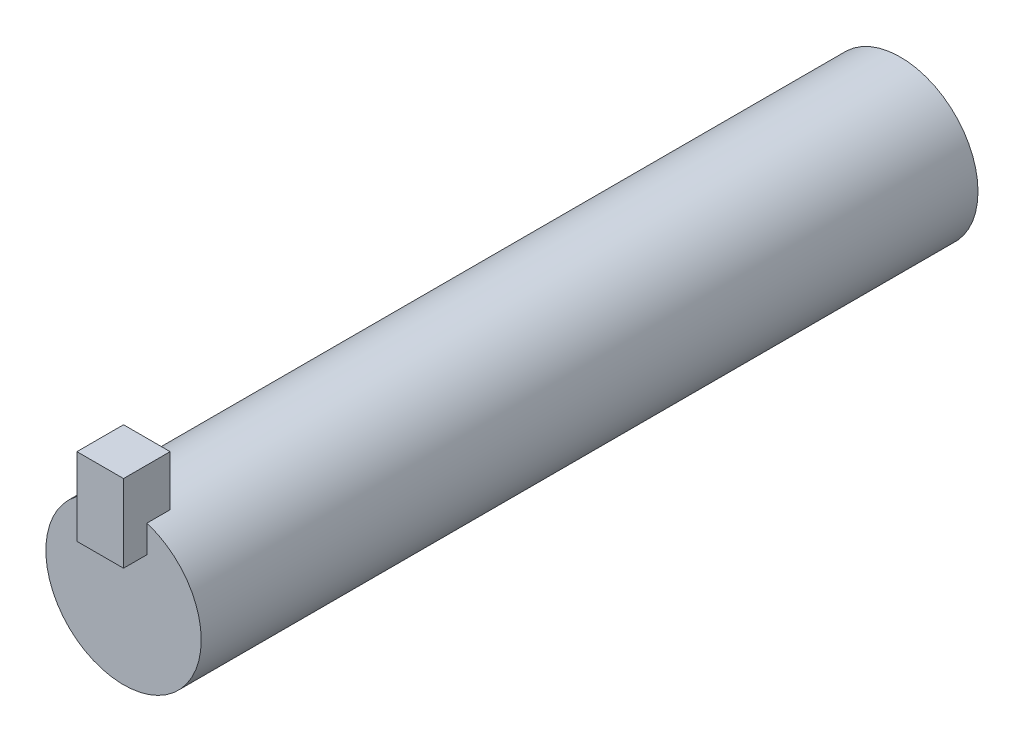
SolidWorks part; units mm, degrees
ref_plane "Ebene vorne" through (0, 0, 0) normal (0, 0, 1) x (1, 0, 0)
ref_plane "Ebene oben" through (0, 0, 0) normal (0, 1, 0) x (1, 0, 0)
ref_plane "Ebene rechts" through (0, 0, 0) normal (1, 0, 0) x (0, 0, -1)
ref_plane "Ebene1" through (0, 5, 0) normal (0, 1, 0) x (1, 0, 0)
sketch "Skizze1" plane through (0, 0, 0) normal (0, 0, 1) x (1, 0, 0)
  circle A0 centre (0, 0) radius 5
  dimension "D1" = 10
extrude "Aufsatz-Linear austragen1" add sketch "Skizze1" along normal blind 50
sketch "Skizze4" plane through (0, 0, 50) normal (0, 0, 1) x (1, 0, 0)
  circle A0 centre (0, 0) radius 5 construction
  circle A1 centre (0, 0) radius 5
curve "Spirale/Helix1" pitch 20 height 45 turns 2.25
sketch "Skizze2" plane through (0, 5, 0) normal (0, 1, 0) x (1, 0, 0)
  line L1 (-2.0776, -40.8531) -> (0.848, -7.4137)
  line L4 (0, -5.6432) -> (0, 5.6432) construction
  dimension "D2" = 5
sketch "Skizze6" plane through (0, 5, 0) normal (0, 1, 0) x (1, 0, 0)
  line L0 (-5, -50) -> (5, -50) construction
  line L1 (0, -5.532) -> (0, 5.532) construction
  circle A0 centre (0, -50) radius 1.5
  dimension "D1" = 3
sketch "Skizze8" plane through (0, 5, 0) normal (0, 1, 0) x (1, 0, 0)
  line L1 (-1.5, -48.5) -> (1.5, -48.5)
  line L2 (-1.5, -48.5) -> (-1.5, -51.5)
  line L3 (-1.5, -51.5) -> (1.5, -51.5)
  line L4 (1.5, -48.5) -> (1.5, -51.5)
  line L5 (-1.5, -48.5) -> (1.5, -51.5) construction
  line L6 (-1.5, -51.5) -> (1.5, -48.5) construction
  point P0 (0, -50)
extrude "Aufsatz-Linear austragen3" add sketch "Skizze8" along normal blind 3 and the other way blind 2 separate body
